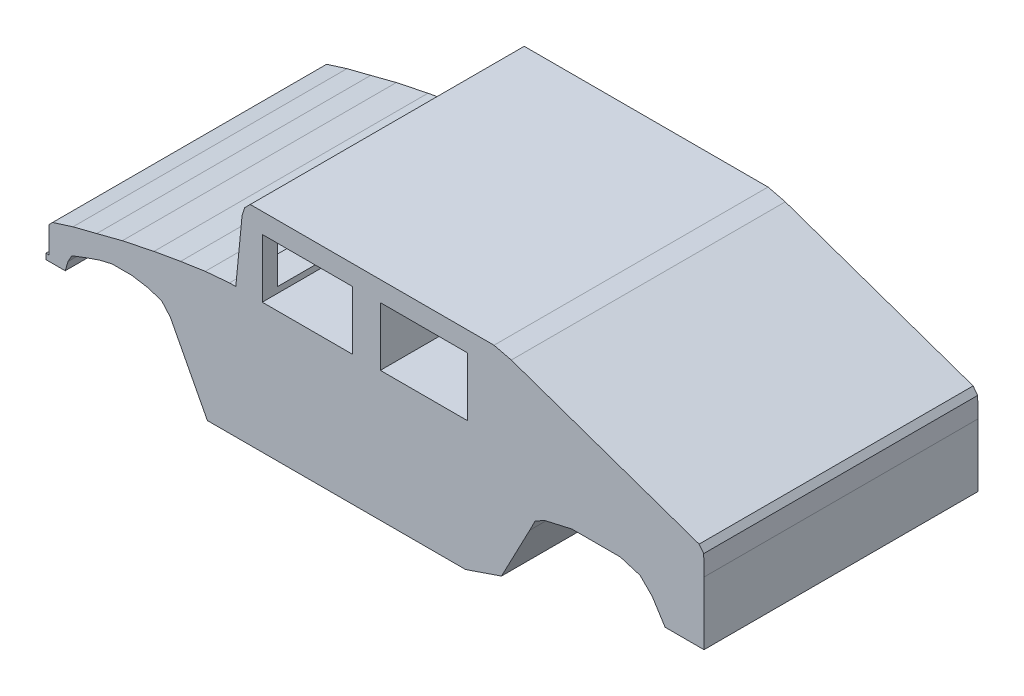
SolidWorks part; units mm, degrees
ref_plane "Front Plane" through (0, 0, 0) normal (0, 0, 1) x (1, 0, 0)
ref_plane "Top Plane" through (0, 0, 0) normal (0, 1, 0) x (1, 0, 0)
ref_plane "Right Plane" through (0, 0, 0) normal (1, 0, 0) x (0, 0, -1)
sketch "Sketch1" plane through (0, 0, 0) normal (0, 0, 1) x (1, 0, 0)
  line L3 (-118.5309, -6.633) -> (-123.3158, -1.2102)
  line L4 (-123.3158, -1.2102) -> (-131.0779, 1.2354)
  line L5 (-131.0779, 1.2354) -> (-139.6906, 2.6177)
  line L6 (-139.6906, 2.6177) -> (-150.43, 2.6177)
  line L7 (-150.43, 2.6177) -> (-157.2351, 1.0227)
  line L8 (-157.2351, 1.0227) -> (-164.5719, -1.5292)
  line L9 (-164.5719, -1.5292) -> (-172.4403, -4.5064)
  line L10 (-172.4403, -4.5064) -> (-174.5669, -8.3343)
  line L11 (-174.5669, -8.3343) -> (-176.0555, -13.4382)
  line L12 (-176.0555, -13.4382) -> (-186.5822, -13.4382)
  line L13 (-186.5822, -13.4382) -> (-186.5822, -10.3546)
  line L14 (-186.5822, -10.3546) -> (-184.8809, -10.3546)
  line L15 (-184.8809, -10.3546) -> (-184.8809, 4.1063)
  line L16 (-184.8809, 4.1063) -> (-182.967, 6.0202)
  line L17 (-182.967, 6.0202) -> (-171.8023, 9.5291)
  line L18 (-171.8023, 9.5291) -> (-158.83, 12.8254)
  line L19 (-158.83, 12.8254) -> (-144.7945, 16.4406)
  line L20 (-144.7945, 16.4406) -> (-127.4627, 20.0558)
  line L21 (-127.4627, 20.0558) -> (-112.8954, 22.6077)
  line L22 (-112.8954, 22.6077) -> (-99.3915, 24.628)
  line L23 (-99.3915, 24.628) -> (-86.1215, 25.7764)
  line L24 (-118.5309, -6.633) -> (-98.2219, -45.5499)
  line L25 (-98.2219, -45.5499) -> (-81.7407, -45.5499)
  line L30 (-81.7407, -45.5499) -> (43.1333, -45.4894)
  line L31 (43.1333, -45.4894) -> (62.7831, -38.7873)
  line L32 (62.7831, -38.7873) -> (78.2223, -9.3126)
  line L33 (78.2223, -9.3126) -> (81.2846, -3.3156)
  line L34 (81.2846, -3.3156) -> (86.7712, -0.5084)
  line L35 (86.7712, -0.5084) -> (101.3172, 2.8091)
  line L36 (101.3172, 2.8091) -> (115.4803, 2.8091)
  line L37 (115.4803, 2.8091) -> (127.8571, 2.8091)
  line L38 (127.8571, 2.8091) -> (138.7028, -0.5084)
  line L39 (138.7028, -0.5084) -> (145.3378, -7.1434)
  line L40 (145.3378, -7.1434) -> (152.3556, -18.2443)
  line L41 (152.3556, -18.2443) -> (173.6642, -18.2443)
  line L42 (173.6642, -18.2443) -> (173.6642, 16.2067)
  line L79 (-86.1215, 25.7764) -> (-82.6764, 25.7764)
  line L80 (-82.6764, 25.7764) -> (-79.2313, 61.2481)
  line L83 (68.1422, 66.3519) -> (58.7001, 68.6487)
  line L84 (58.7001, 68.6487) -> (-74.7655, 68.6487)
  line L85 (-74.7655, 68.6487) -> (-77.8278, 65.5863)
  line L86 (-77.8278, 65.5863) -> (-79.2313, 61.2481)
  line L87 (68.1422, 66.3519) -> (170.9846, 30.4974)
  line L88 (170.9846, 30.4974) -> (173.4888, 27.2437)
  line L89 (173.4888, 27.2437) -> (173.6642, 16.2067)
extrude "Extrude1" add sketch "Sketch1" along normal blind 150
sketch "Sketch2" plane through (0, 0, 150) normal (0, 0, 1) x (1, 0, 0)
  line L1 (-68.1734, 57.7439) -> (-18.8749, 57.7439)
  line L2 (-68.1734, 57.7439) -> (-68.1734, 25.6086)
  line L3 (-68.1734, 25.6086) -> (-18.8749, 25.6086)
  line L4 (-18.8749, 57.7439) -> (-18.8749, 25.6086)
  line L5 (-3.5376, 57.7439) -> (44.3002, 57.7439)
  line L6 (-3.5376, 57.7439) -> (-3.5376, 25.6086)
  line L7 (-3.5376, 25.6086) -> (44.3002, 25.6086)
  line L8 (44.3002, 57.7439) -> (44.3002, 25.6086)
extrude "Cut-Extrude1" cut sketch "Sketch2" against normal blind 150
sketch "Sketch3" plane through (-84.3839, 8.1956, 0) normal (-0.9953, 0.0967, 0) x (0, 0, 1)
  line L1 (6.7619, 49.2007) -> (141.7606, 49.2007)
  line L2 (6.7619, 49.2007) -> (6.7619, 22.1085)
  line L3 (6.7619, 22.1085) -> (141.7606, 22.1085)
  line L4 (141.7606, 49.2007) -> (141.7606, 22.1085)
extrude "Cut-Extrude2" cut sketch "Sketch3" against normal blind 20
